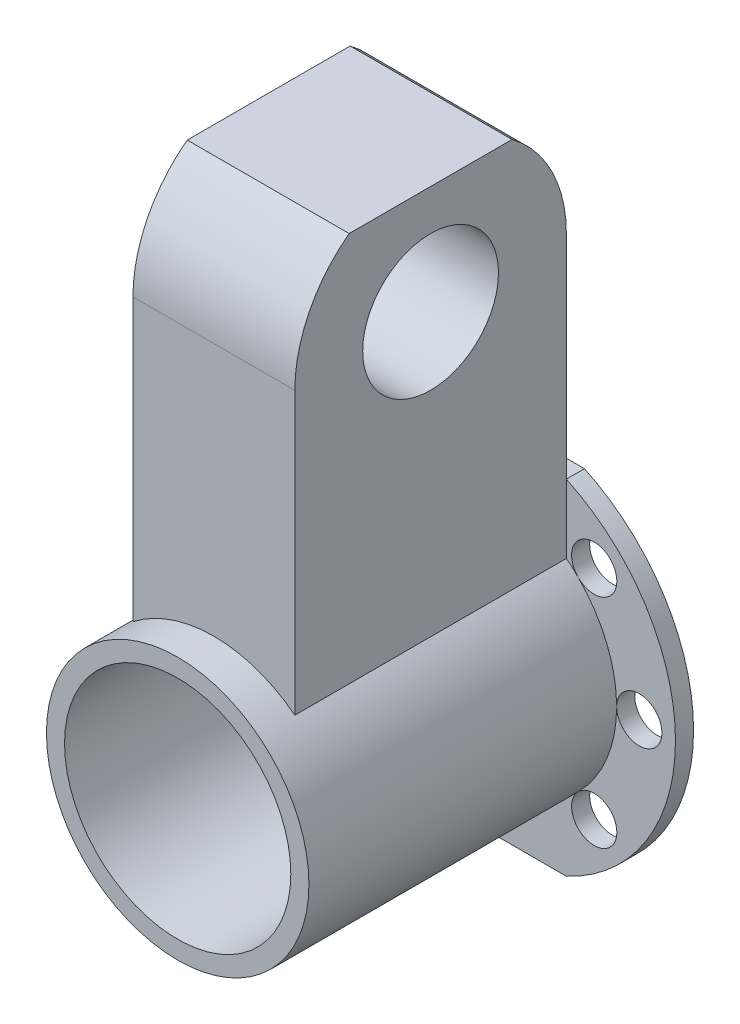
SolidWorks part; units mm, degrees
ref_plane "Ön Düzlem" through (0, 0, 0) normal (0, 0, 1) x (1, 0, 0)
ref_plane "Üst Düzlem" through (0, 0, 0) normal (0, 1, 0) x (1, 0, 0)
ref_plane "Sağ Düzlem" through (0, 0, 0) normal (1, 0, 0) x (0, 0, -1)
sketch "Çizim1" plane through (0, 0, 0) normal (0, 0, 1) x (1, 0, 0)
  circle A0 centre (0, 0) radius 12.5
  circle A2 centre (0, 0) radius 14.5
  dimension "D1" = 25
  dimension "D2" = 2
  dimension "D3" = 29
extrude "Yükseklik-Ekstrüzyon1" add sketch "Çizim1" along normal blind 34
sketch "Çizim2" plane through (0, 0, 0) normal (0, 0, -1) x (-1, 0, 0)
  circle A0 centre (0, 0) radius 21
  circle A3 centre (0, 0) radius 12.5 construction
  circle A4 centre (0, 0) radius 12.5
  dimension "D1" = 42
extrude "Yükseklik-Ekstrüzyon2" add sketch "Çizim2" along normal blind 2 separate body
sketch "Çizim3" plane through (0, 0, -2) normal (0, 0, -1) x (-1, 0, 0)
  circle A0 centre (-17, 0) radius 2.5
  circle A1 centre (-12.0208, 12.0208) radius 2.5
  circle A3 centre (12.0208, 12.0208) radius 2.5
  circle A4 centre (17, 0) radius 2.5
  circle A5 centre (12.0208, -12.0208) radius 2.5
  circle A7 centre (-12.0208, -12.0208) radius 2.5
  circle A8 centre (0, 17) radius 2.5 [skipped]
  circle A9 centre (0, -17) radius 2.5 [skipped]
  point P19 (0, 0)
  dimension "D2" = 5
  dimension "D1" = 17
  dimension "D3" = 8
extrude "Kes-Ekstrüzyon1" cut sketch "Çizim3" against normal blind 78
sketch "Çizim4" plane through (0, 0, -2) normal (0, 0, -1) x (-1, 0, 0)
  line L0 (-8.9443, 19) -> (8.9443, 19)
  line L1 (-8.9443, -19) -> (8.9443, -19)
  circle A0 centre (0, 0) radius 21 construction
  arc A1 (-8.9443, -19) -> (8.9443, -19) centre (0, 0) ccw
  arc A2 (8.9443, 19) -> (-8.9443, 19) centre (0, 0) ccw
  dimension "D1" = 19
  dimension "D2" = 19
extrude "Kes-Ekstrüzyon2" cut sketch "Çizim4" against normal blind 78
ref_plane "Düzlem1" through (0, 14.5, 0) normal (0, 1, 0) x (0, 0, -1)
sketch "Çizim6" plane through (0, 14.5, 0) normal (0, 1, 0) x (0, 0, -1)
  line L0 (0, 8.9443) -> (0, -8.9443)
  line L1 (0, 8.9443) -> (-30, 8.9443)
  line L2 (0, -8.9443) -> (-30, -8.9443)
  line L3 (-30, 8.9443) -> (-30, -8.9443)
  line L4 (0, 8.9443) -> (-30, -8.9443) construction
  line L5 (0, -8.9443) -> (-30, 8.9443) construction
  line L8 (2, -8.9443) -> (0, -8.9443) construction
  line L9 (0, -14.5) -> (0, 14.5) construction
  point P0 (0, 0)
  point P1 (-15, 0)
  dimension "D1" = 30
extrude "Yükseklik-Ekstrüzyon5" add sketch "Çizim6" against normal up to surface up to face at (14.5, 0, 34)
sketch "Çizim9" plane through (0, 14.5, 0) normal (0, 1, 0) x (1, 0, 0)
  line L5 (-8.9443, -30) -> (0, -30)
  line L6 (0, -30) -> (8.9443, -30)
  line L7 (8.9443, -30) -> (8.9443, 0)
  line L8 (8.9443, 0) -> (-8.9443, 0)
  line L9 (-8.9443, 0) -> (-8.9443, -30)
  line L10 (-8.9443, -30) -> (0, -30)
  line L11 (0, -30) -> (8.9443, -30)
  line L12 (8.9443, -30) -> (8.9443, 0)
  line L13 (8.9443, 0) -> (-8.9443, 0)
  line L14 (-8.9443, 0) -> (-8.9443, -30)
  dimension "D1" = 0
extrude "Yükseklik-Ekstrüzyon6" add sketch "Çizim9" along normal blind 40
sketch "Çizim10" plane through (-8.9443, 0, 0) normal (-1, 0, 0) x (0, 0, 1)
  line L0 (0, 54.5) -> (30, 54.5) construction
  line L1 (30, 11.4127) -> (30, 54.5) construction
  circle A0 centre (15, 42.5) radius 7.5
  dimension "D1" = 15
  dimension "D2" = 12
  dimension "D3" = 15
extrude "Kes-Ekstrüzyon3" cut sketch "Çizim10" against normal blind 30
sketch "Çizim11" plane through (-8.9443, 0, 0) normal (-1, 0, 0) x (0, 0, 1)
  line L0 (30, 11.4127) -> (30, 54.5) construction
  line L1 (0, 54.5) -> (30, 54.5) construction
  line L2 (0, 54.5) -> (0, 19) construction
  line L3 (30, 42.5) -> (30, 54.5)
  line L4 (0, 54.5) -> (6, 54.5)
  line L5 (0, 54.5) -> (0, 42.5)
  line L6 (24, 54.5) -> (30, 54.5)
  arc A0 (30, 42.5) -> (24, 54.5) centre (15, 42.5) ccw
  arc A1 (6, 54.5) -> (0, 42.5) centre (15, 42.5) ccw
extrude "Kes-Ekstrüzyon4" cut sketch "Çizim11" against normal blind 93
